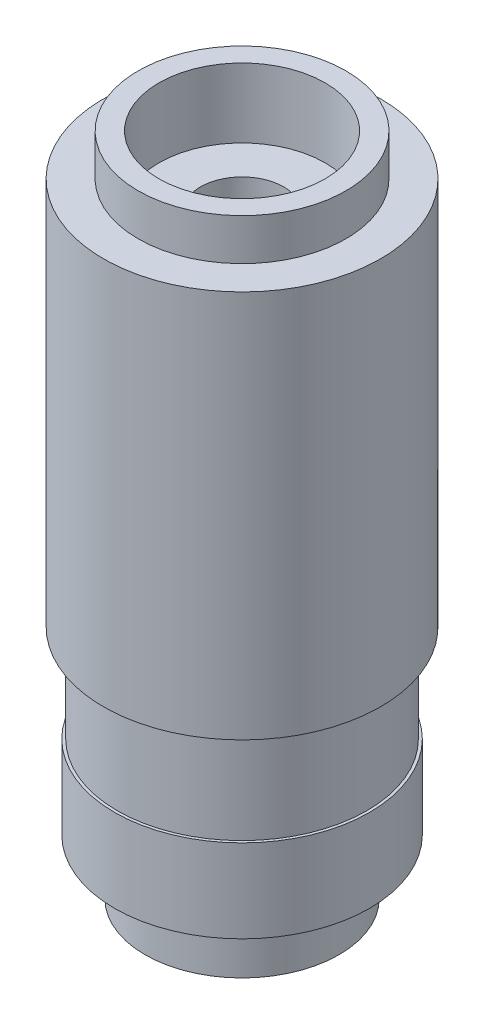
SolidWorks part; units mm, degrees
ref_plane "Спереди" through (0, 0, 0) normal (0, 0, 1) x (1, 0, 0)
ref_plane "Сверху" through (0, 0, 0) normal (0, 1, 0) x (1, 0, 0)
ref_plane "Справа" through (0, 0, 0) normal (1, 0, 0) x (0, 0, -1)
sketch "Эскиз1" plane through (0, 0, 0) normal (0, 0, 1) x (1, 0, 0)
  line L0 (0, 0) -> (0, 26.6194) construction
  line L1 (3.5, 0) -> (1.8, 0)
  line L2 (1.5, 4.2927) -> (1.5, 21.5)
  line L3 (1.5, 21.5) -> (3, 21.5)
  line L4 (3.75, 24) -> (3.75, 22.5)
  line L5 (3.75, 22.5) -> (5, 22.5)
  line L6 (5, 22.5) -> (5, 8.5)
  line L7 (4.6, 2) -> (3.5, 2)
  line L8 (3.5, 2) -> (3.5, 0)
  line L9 (1.5, 4.2927) -> (1.8, 4)
  line L10 (1.8, 4) -> (1.8, 0)
  line L11 (3, 21.5) -> (3, 24)
  line L12 (4.6, 5) -> (4.6, 2)
  line L13 (4.5, 5) -> (4.6, 5)
  line L14 (3, 24) -> (3.75, 24)
  line L15 (4.5, 8.5) -> (4.5, 5)
  line L16 (5, 8.5) -> (4.5, 8.5)
  dimension "D2" = 7.5
  dimension "D3" = 10
  dimension "D4" = 2.5
  dimension "D5" = 2
  dimension "D6" = 7
  dimension "D7" = 24
  dimension "D8" = 3.6
  dimension "D9" = 4
  dimension "D10" = 1.5
  dimension "D11" = 6
  dimension "D12" = 3
  dimension "D13" = 9.2
  dimension "D14" = 9
  dimension "D15" = 3.5
  dimension "D16" = 3
revolve "Повернуть1" add sketch "Эскиз1" angle 360 about L0
sketch "Эскиз3" plane through (0, 0, 0) normal (0, -1, 0) x (1, 0, 0)
  line L0 (0.047, 1.7994) -> (0.3129, 1.9754)
  line L1 (-0.047, 1.7994) -> (-0.3129, 1.9754)
  line L2 (0, 0) -> (-0.3129, 1.9754) construction
  line L3 (0.3129, 1.9754) -> (0, 0) construction
  line L4 (0.5114, 1.7258) -> (0.3129, 1.9754)
  line L5 (0.6007, 1.6968) -> (0.908, 1.782)
  line L6 (1.0196, 1.4833) -> (0.908, 1.782)
  line L7 (1.0957, 1.4281) -> (1.4142, 1.4142)
  line L8 (1.4281, 1.0957) -> (1.4142, 1.4142)
  line L9 (1.4833, 1.0196) -> (1.782, 0.908)
  line L10 (1.6968, 0.6007) -> (1.782, 0.908)
  line L11 (1.7258, 0.5114) -> (1.9754, 0.3129)
  line L12 (1.7994, 0.047) -> (1.9754, 0.3129)
  line L13 (1.7994, -0.047) -> (1.9754, -0.3129)
  line L14 (1.7258, -0.5114) -> (1.9754, -0.3129)
  line L15 (1.6968, -0.6007) -> (1.782, -0.908)
  line L16 (1.4833, -1.0196) -> (1.782, -0.908)
  line L17 (1.4281, -1.0957) -> (1.4142, -1.4142)
  line L18 (1.0957, -1.4281) -> (1.4142, -1.4142)
  line L19 (1.0196, -1.4833) -> (0.908, -1.782)
  line L20 (0.6007, -1.6968) -> (0.908, -1.782)
  line L21 (0.5114, -1.7258) -> (0.3129, -1.9754)
  line L22 (0.047, -1.7994) -> (0.3129, -1.9754)
  line L23 (-0.047, -1.7994) -> (-0.3129, -1.9754)
  line L24 (-0.5114, -1.7258) -> (-0.3129, -1.9754)
  line L25 (-0.6007, -1.6968) -> (-0.908, -1.782)
  line L26 (-1.0196, -1.4833) -> (-0.908, -1.782)
  line L27 (-1.0957, -1.4281) -> (-1.4142, -1.4142)
  line L28 (-1.4281, -1.0957) -> (-1.4142, -1.4142)
  line L29 (-1.4833, -1.0196) -> (-1.782, -0.908)
  line L30 (-1.6968, -0.6007) -> (-1.782, -0.908)
  line L31 (-1.7258, -0.5114) -> (-1.9754, -0.3129)
  line L32 (-1.7994, -0.047) -> (-1.9754, -0.3129)
  line L33 (-1.7994, 0.047) -> (-1.9754, 0.3129)
  line L34 (-1.7258, 0.5114) -> (-1.9754, 0.3129)
  line L35 (-1.6968, 0.6007) -> (-1.782, 0.908)
  line L36 (-1.4833, 1.0196) -> (-1.782, 0.908)
  line L37 (-1.4281, 1.0957) -> (-1.4142, 1.4142)
  line L38 (-1.0957, 1.4281) -> (-1.4142, 1.4142)
  line L39 (-1.0196, 1.4833) -> (-0.908, 1.782)
  line L40 (-0.6007, 1.6968) -> (-0.908, 1.782)
  line L41 (-0.5114, 1.7258) -> (-0.3129, 1.9754)
  circle A0 centre (0, 0) radius 2 construction
  circle A1 centre (0, 0) radius 1.8 construction
  arc A2 (-0.047, 1.7994) -> (0.047, 1.7994) centre (0, 0) cw
  arc A3 (0.5114, 1.7258) -> (0.6007, 1.6968) centre (0, 0) cw
  arc A4 (1.0196, 1.4833) -> (1.0957, 1.4281) centre (0, 0) cw
  arc A5 (1.4281, 1.0957) -> (1.4833, 1.0196) centre (0, 0) cw
  arc A6 (1.6968, 0.6007) -> (1.7258, 0.5114) centre (0, 0) cw
  arc A7 (1.7994, 0.047) -> (1.7994, -0.047) centre (0, 0) cw
  arc A8 (1.7258, -0.5114) -> (1.6968, -0.6007) centre (0, 0) cw
  arc A9 (1.4833, -1.0196) -> (1.4281, -1.0957) centre (0, 0) cw
  arc A10 (1.0957, -1.4281) -> (1.0196, -1.4833) centre (0, 0) cw
  arc A11 (0.6007, -1.6968) -> (0.5114, -1.7258) centre (0, 0) cw
  arc A12 (0.047, -1.7994) -> (-0.047, -1.7994) centre (0, 0) cw
  arc A13 (-0.5114, -1.7258) -> (-0.6007, -1.6968) centre (0, 0) cw
  arc A14 (-1.0196, -1.4833) -> (-1.0957, -1.4281) centre (0, 0) cw
  arc A15 (-1.4281, -1.0957) -> (-1.4833, -1.0196) centre (0, 0) cw
  arc A16 (-1.6968, -0.6007) -> (-1.7258, -0.5114) centre (0, 0) cw
  arc A17 (-1.7994, -0.047) -> (-1.7994, 0.047) centre (0, 0) cw
  arc A18 (-1.7258, 0.5114) -> (-1.6968, 0.6007) centre (0, 0) cw
  arc A19 (-1.4833, 1.0196) -> (-1.4281, 1.0957) centre (0, 0) cw
  arc A20 (-1.0957, 1.4281) -> (-1.0196, 1.4833) centre (0, 0) cw
  arc A21 (-0.6007, 1.6968) -> (-0.5114, 1.7258) centre (0, 0) cw
  dimension "D1" = 3.6
  dimension "D2" = 4
  dimension "D3" = 113
  dimension "D4" = 18
  dimension "D5" = 20
extrude "Вырез-Вытянуть1" cut sketch "Эскиз3" against normal blind 3
